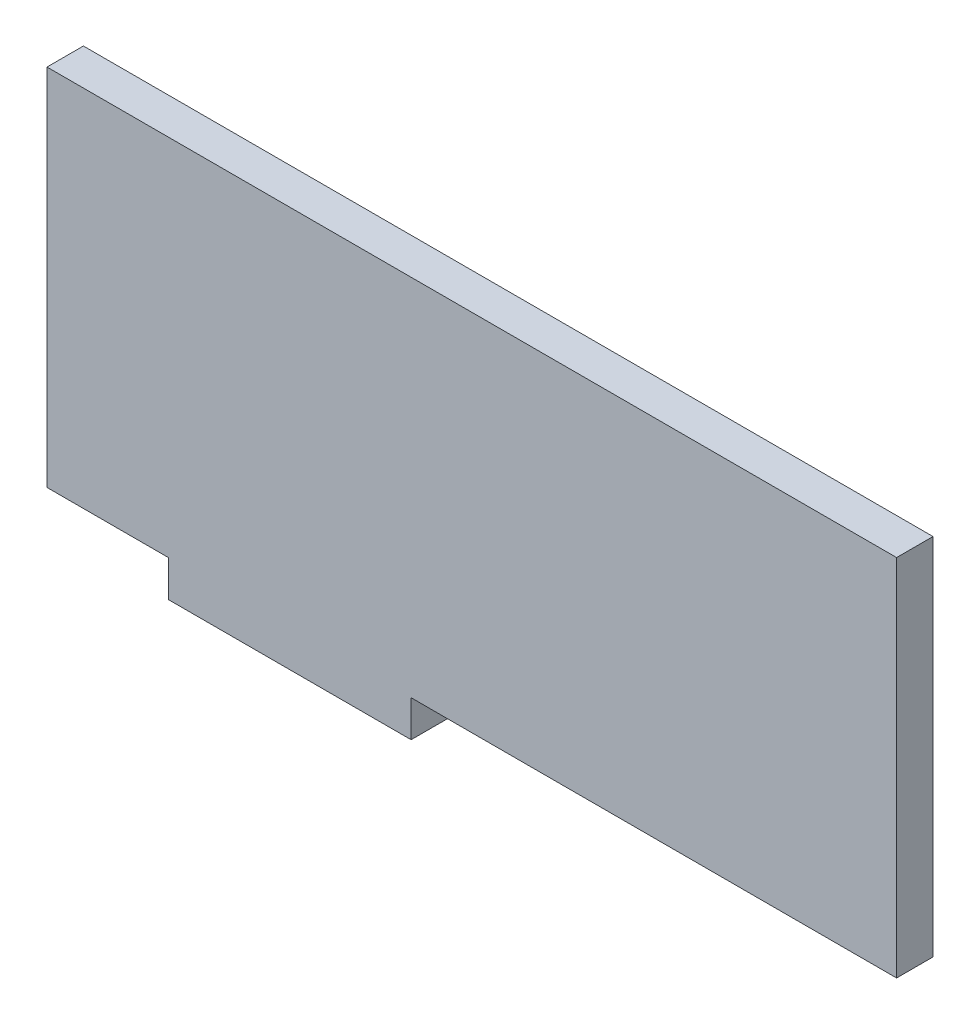
SolidWorks part; units mm, degrees
ref_plane "Front Plane" through (0, 0, 0) normal (0, 0, 1) x (1, 0, 0)
ref_plane "Top Plane" through (0, 0, 0) normal (0, 1, 0) x (1, 0, 0)
ref_plane "Right Plane" through (0, 0, 0) normal (1, 0, 0) x (0, 0, -1)
sketch "Sketch1" plane through (0, 0, 0) normal (0, 0, 1) x (1, 0, 0)
  line L0 (0, 0) -> (-10, 0)
  line L1 (-10, 0) -> (-10, 30)
  line L2 (-10, 30) -> (60, 30)
  line L3 (60, 30) -> (60, 0)
  line L4 (60, 0) -> (20, 0)
  line L5 (20, 0) -> (20, -3)
  line L6 (20, -3) -> (0, -3)
  line L7 (0, -3) -> (0, 0)
  dimension "D1" = 30
  dimension "D2" = 10
  dimension "D3" = 40
  dimension "D4" = 20
  dimension "D5" = 3
extrude "Boss-Extrude1" add sketch "Sketch1" along normal blind 3
